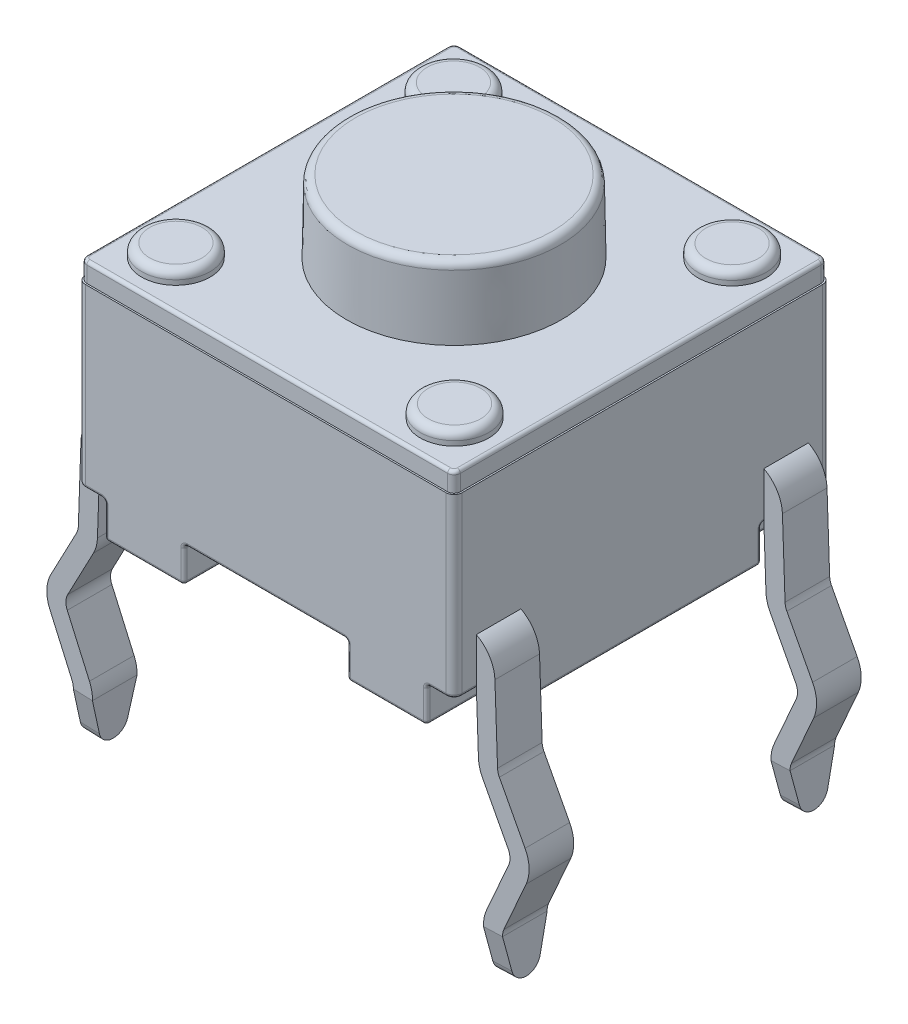
SolidWorks part; units mm, degrees
ref_plane "Front Plane" through (0, 0, 0) normal (0, 0, 1) x (1, 0, 0)
ref_plane "Top Plane" through (0, 0, 0) normal (0, 1, 0) x (1, 0, 0)
ref_plane "Right Plane" through (0, 0, 0) normal (1, 0, 0) x (0, 0, -1)
sketch "Sketch1" plane through (0, 0, 0) normal (0, 1, 0) x (1, 0, 0)
  line L1 (-3.0035, -3.0035) -> (3.0035, -3.0035)
  line L2 (-3.0035, -3.0035) -> (-3.0035, 3.0036)
  line L3 (-3.0035, 3.0036) -> (3.0035, 3.0036)
  line L4 (3.0035, -3.0035) -> (3.0035, 3.0036)
  line L5 (-3.0035, -3.0035) -> (3.0035, 3.0036) construction
  line L6 (-3.0035, 3.0036) -> (3.0035, -3.0035) construction
  point P0 (0, 0)
  dimension "D1" = 6.0071
  dimension "D2" = 6.0071
extrude "Boss-Extrude1" add sketch "Sketch1" along normal blind 2.8194 from offset 0.5588
fillet "Fillet1" radius 0.127 4 edges at (-3.0035, 1.9685, 3.0035) (-3.0035, 1.9685, -3.0036) (3.0035, 1.9685, -3.0036) (3.0035, 1.9685, 3.0035)
sketch "Sketch2" plane through (0, 3.3782, 0) normal (0, -1, 0) x (-1, 0, 0)
  line L8 (2.9781, -2.8765) -> (2.9781, 2.8765)
  line L9 (-2.8765, -2.9781) -> (2.8765, -2.9781)
  line L10 (-2.9781, 2.8765) -> (-2.9781, -2.8765)
  line L11 (2.8765, 2.9782) -> (-2.8765, 2.9782)
  line L12 (2.9781, -2.8765) -> (2.9781, 2.8765)
  line L13 (-2.8765, -2.9781) -> (2.8765, -2.9781)
  line L14 (-2.9781, 2.8765) -> (-2.9781, -2.8765)
  line L15 (2.8765, 2.9782) -> (-2.8765, 2.9782)
  arc A8 (2.8765, -2.9781) -> (2.9781, -2.8765) centre (2.8765, -2.8765) ccw
  arc A9 (-2.9781, -2.8765) -> (-2.8765, -2.9781) centre (-2.8765, -2.8765) ccw
  arc A10 (-2.8765, 2.9782) -> (-2.9781, 2.8765) centre (-2.8765, 2.8766) ccw
  arc A11 (2.9781, 2.8765) -> (2.8765, 2.9782) centre (2.8765, 2.8765) ccw
  arc A12 (2.8765, -2.9781) -> (2.9781, -2.8765) centre (2.8765, -2.8765) ccw
  arc A13 (-2.9781, -2.8765) -> (-2.8765, -2.9781) centre (-2.8765, -2.8765) ccw
  arc A14 (-2.8765, 2.9782) -> (-2.9781, 2.8765) centre (-2.8765, 2.8766) ccw
  arc A15 (2.9781, 2.8765) -> (2.8765, 2.9782) centre (2.8765, 2.8765) ccw
  dimension "D1" = 0.0254
extrude "Boss-Extrude2" add sketch "Sketch2" against normal blind 0.3048
sketch "Sketch3" plane through (0, 0, 0) normal (0, 1, 0) x (1, 0, 0)
  line L0 (-2.5662, -3.0035) -> (-2.5662, -1.8948)
  line L1 (-2.8765, -3.0035) -> (2.8765, -3.0035) construction
  line L2 (-2.5662, -1.8948) -> (-3.0035, -1.8948)
  line L3 (-3.0035, 2.8765) -> (-3.0035, -2.8765) construction
  line L4 (-2.4413, -0.5609) -> (-1.3018, -0.5609)
  line L5 (-1.3018, -0.5609) -> (-1.3017, -3.0035)
  line L6 (-2.4413, -0.5609) -> (-2.4413, 0.5609)
  line L7 (-2.5662, -3.0035) -> (-1.3017, -3.0035)
  line L8 (-3.0035, -1.8948) -> (-3.0035, 1.8948)
  line L9 (-2.4413, 0) -> (-3.0035, 0) construction
  line L10 (-2.5662, 3.0036) -> (-1.3017, 3.0035)
  line L11 (-1.3017, 0.5609) -> (-1.3017, 3.0035)
  line L12 (-2.4413, 0.5609) -> (-1.3017, 0.5609)
  line L13 (-2.5662, 1.8948) -> (-3.0035, 1.8948)
  line L14 (-2.5662, 3.0036) -> (-2.5662, 1.8948)
  line L15 (0, -3.0035) -> (0, 3.0036) construction
  line L16 (2.8765, 3.0036) -> (-2.8765, 3.0036) construction
  line L17 (2.4413, 0) -> (3.0035, 0) construction
  line L18 (2.5662, 3.0035) -> (2.5662, 1.8948)
  line L19 (2.5662, 1.8948) -> (3.0035, 1.8948)
  line L20 (2.4413, 0.5609) -> (1.3017, 0.5609)
  line L21 (1.3017, 0.5609) -> (1.3017, 3.0035)
  line L22 (2.5662, 3.0035) -> (1.3017, 3.0035)
  line L23 (3.0035, -1.8948) -> (3.0035, 1.8948)
  line L24 (2.5662, -3.0036) -> (1.3017, -3.0036)
  line L25 (2.4413, -0.5609) -> (2.4413, 0.5609)
  line L26 (1.3017, -0.5609) -> (1.3017, -3.0036)
  line L27 (2.4413, -0.5609) -> (1.3017, -0.5609)
  line L28 (2.5662, -1.8948) -> (3.0035, -1.8948)
  line L29 (2.5662, -3.0036) -> (2.5662, -1.8948)
  dimension "D1" = 1.7018
extrude "Boss-Extrude3" add sketch "Sketch3" along normal up to next
sketch "Sketch4" plane through (0, 3.683, 0) normal (0, 1, 0) x (1, 0, 0)
  line L1 (-2.2217, -2.2129) -> (2.2217, -2.2129) construction
  line L2 (-2.2217, -2.2129) -> (-2.2217, 2.2129) construction
  line L3 (-2.2217, 2.2129) -> (2.2217, 2.2129) construction
  line L4 (2.2217, -2.2129) -> (2.2217, 2.2129) construction
  line L5 (-2.2217, -2.2129) -> (2.2217, 2.2129) construction
  line L6 (-2.2217, 2.2129) -> (2.2217, -2.2129) construction
  circle A0 centre (2.2217, 2.2129) radius 0.5461
  circle A1 centre (-2.2217, 2.2129) radius 0.5461
  circle A2 centre (-2.2217, -2.2129) radius 0.5461
  circle A3 centre (2.2217, -2.2129) radius 0.5461
  point P0 (0, 0)
  dimension "D1" = 1.0922
extrude "Boss-Extrude4" add sketch "Sketch4" along normal blind 0.2032
sketch "Sketch5" plane through (0, 3.683, 0) normal (0, 1, 0) x (1, 0, 0)
  circle A0 centre (0, 0) radius 1.7145
  dimension "D1" = 3.429
extrude "Boss-Extrude5" add sketch "Sketch5" along normal blind 1.15 draft 1
fillet "Fillet2" radius 0.127 5 edges at (-2.2217, 3.8862, -1.6668) (-2.2217, 3.8862, 2.759) (2.2217, 3.8862, -1.6668) (2.2217, 3.8862, 2.759) (0, 4.833, 1.6944)
fillet "Fillet3" radius 0.0508 88 edges at (2.9664, 0.5588, 2.9664) (2.9664, 0.5588, -2.9664) (-2.9664, 0.5588, -2.9664) (-2.9664, 0.5588, 2.9664) (3.0035, 0.5588, 2.3857) (3.0035, 0.5588, -2.3857) (1.3017, 0.2794, 3.0036) (1.3017, 0.2794, -3.0035) (2.9484, 3.683, -2.9484) (0, 3.683, -2.9782) (-2.9484, 3.683, -2.9484) (-2.9781, 3.683, 0) (-2.9484, 3.683, 2.9484) (0, 3.683, 2.9781) (2.9484, 3.683, 2.9484) (2.4413, 0.2794, 0.5609) (1.3017, 0.2794, 0.5609) (1.3017, 0.2794, -0.5609) (2.4413, 0.2794, -0.5609) (-1.3018, 0.2794, 0.5609) (-2.4413, 0.2794, 0.5609) (-2.4413, 0.2794, -0.5609) (-1.3017, 0.2794, -0.5609) (2.7849, 0.5588, 1.8948) (3.0035, 0.2794, 1.8948) (2.5662, 0.2794, 3.0036) (2.5662, 0.5588, 2.4492) (2.5662, 0.2794, 1.8948) (3.0035, 0.2794, -1.8948) (2.7849, 0.5588, -1.8948) (2.5662, 0.2794, -1.8948) (2.5662, 0.5588, -2.4492) (2.5662, 0.2794, -3.0035) (-2.5662, 0.2794, -1.8948) (-2.5662, 0.2794, 1.8948) (-1.8715, 0.5588, -0.5609) (-2.4413, 0.5588, 0) (-1.8715, 0.5588, 0.5609) (1.3017, 0.5588, 1.7822) (1.8715, 0.5588, 0.5609) (2.4413, 0.5588, 0) (1.8715, 0.5588, -0.5609) (1.3017, 0.5588, -1.7822) (-1.3017, 0, 1.7822) (-1.8715, 0, 0.5609) (-2.4413, 0, 0) (-1.8715, 0, -0.5609) (-1.3017, 0, -1.7822) (-1.934, 0, -3.0035) (-2.5662, 0, -2.4492) (-2.7849, 0, -1.8948) (-3.0035, 0, 0) (-2.7849, 0, 1.8948) (-2.5662, 0, 2.4492) (-1.934, 0, 3.0035) (1.3017, 0, -1.7822) (1.8715, 0, -0.5609) (2.4413, 0, 0) (1.8715, 0, 0.5609) (1.3017, 0, 1.7822) (1.934, 0, 3.0036) (2.5662, 0, 2.4492) (2.7849, 0, 1.8948) (3.0035, 0, 0) (2.7849, 0, -1.8948) (2.5662, 0, -2.4492) (1.934, 0, -3.0035) (2.9781, 3.683, 0)
sketch "Sketch6" plane through (0, 0, 3.0035) normal (0, 0, 1) x (1, 0, 0)
  line L0 (-2.9873, 1.0641) -> (-3.0423, -0.5107)
  line L1 (-3.0423, -0.5107) -> (-3.5687, -1.5089)
  line L2 (-3.5687, -1.5089) -> (-3.1132, -2.5415)
  line L3 (-3.1132, -2.5415) -> (-3.1424, -3.3782)
  line L4 (-2.9873, 1.0641) -> (-2.5265, 1.0641)
  line L5 (-1.3525, 0) -> (-2.5154, 0) construction
  dimension "D1" = 4.445
  dimension "D2" = 3.3782
  dimension "D3" = 3.0226
  dimension "D4" = 3.5687
  dimension "D5" = 2.032
  dimension "D6" = 1.5748
  dimension "D7" = 92
extrude "Extrude-Thin1" add sketch "Sketch6" against normal blind 0.7112 from offset 0.3556 thin offset against normal yes
sketch "Sketch9" plane through (-3.3254, 0.1161, 0) normal (-0.9994, 0.0349, 0) x (0, 0, 1)
  line L0 (2.6479, -2.7766) -> (2.5175, -3.3091)
  line L1 (2.0672, -3.3091) -> (1.9367, -2.7766)
  line L2 (1.9367, -3.4858) -> (2.6479, -3.4858) construction
  line L3 (2.6479, -2.7766) -> (2.6479, -3.4858)
  line L4 (2.6479, -3.4858) -> (1.9367, -3.4858)
  line L5 (1.9367, -3.4858) -> (1.9367, -2.7766)
  arc A0 (2.5175, -3.3091) -> (2.0672, -3.3091) centre (2.2923, -3.254) cw
  line M1 (2.6479, -3.4858) -> (2.6479, -2.7766)
  line M3 (1.9367, -2.7766) -> (1.9367, -3.4858)
  line M4 (1.9367, -3.4858) -> (2.6479, -3.4858)
extrude "Cut-Extrude1" cut sketch "Sketch9" against normal blind 0.7112 contours L0 A0 L4 M1 | A0 L1 M4 M3
mirror "Mirror1" about plane through (0, 0, 0) normal (0, 0, 1) of "Cut-Extrude1", "Extrude-Thin1"
mirror "Mirror3" about plane through (0, 0, 0) normal (1, 0, 0) of "Mirror1", "Cut-Extrude1", "Extrude-Thin1"
